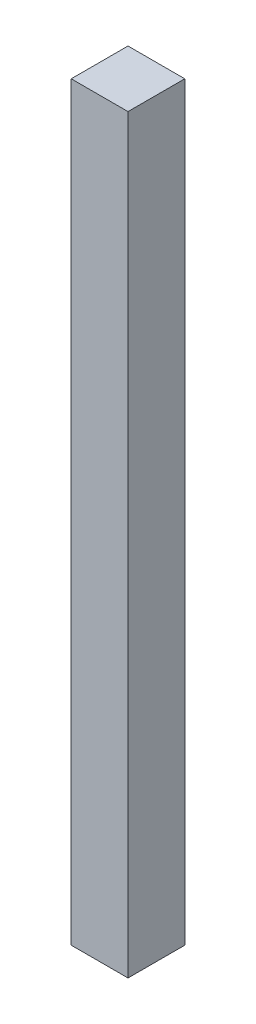
SolidWorks part; units mm, degrees
ref_plane "Front Plane" through (0, 0, 0) normal (0, 0, 1) x (1, 0, 0)
ref_plane "Top Plane" through (0, 0, 0) normal (0, 1, 0) x (1, 0, 0)
ref_plane "Right Plane" through (0, 0, 0) normal (1, 0, 0) x (0, 0, -1)
sketch "Sketch1" plane through (0, 0, 0) normal (0, 1, 0) x (1, 0, 0)
  line L0 (0, 0) -> (0, 88.9)
  line L1 (0, 88.9) -> (-88.9, 88.9)
  line L2 (-88.9, 88.9) -> (-88.9, 0)
  line L3 (-88.9, 0) -> (0, 0)
  dimension "D1" = 88.9
  dimension "D2" = 88.9
extrude "Boss-Extrude1" add sketch "Sketch1" along normal blind 1174.75 contours L1 L2 L3 L0
